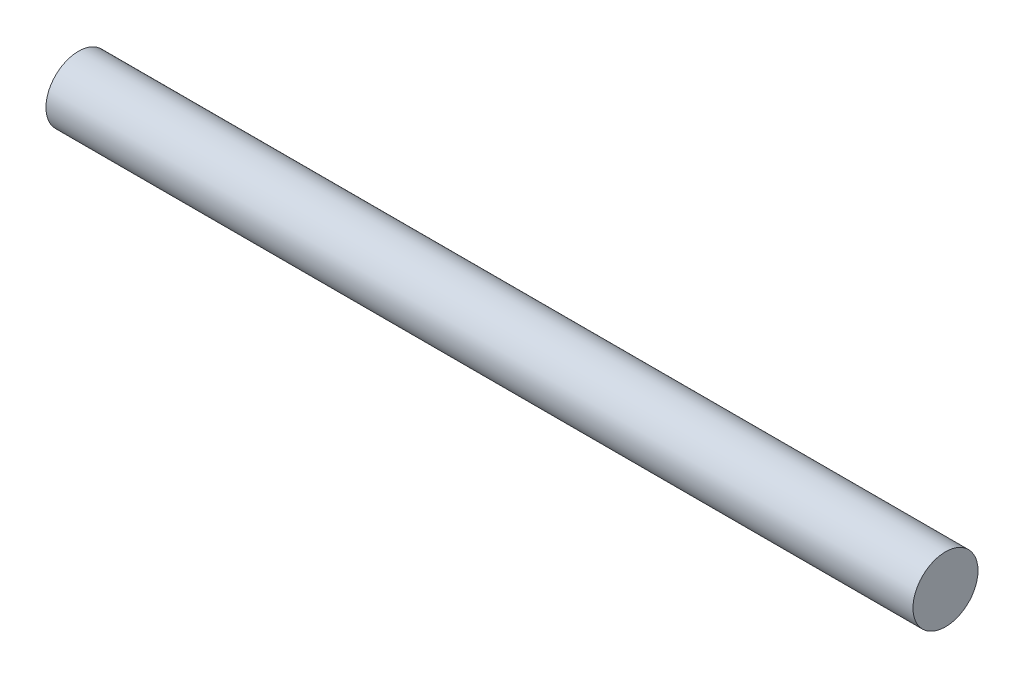
SolidWorks part; units mm, degrees
material "6061-T6 (SS)"
ref_plane "Front Plane" through (0, 0, 0) normal (0, 0, 1) x (1, 0, 0)
ref_plane "Top Plane" through (0, 0, 0) normal (0, 1, 0) x (1, 0, 0)
ref_plane "Right Plane" through (0, 0, 0) normal (1, 0, 0) x (0, 0, -1)
sketch "Sketch1" plane through (0, 0, 0) normal (1, 0, 0) x (0, 0, -1)
  circle A0 centre (0, 0) radius 4.7625
  dimension "D1" = 9.525
extrude "Boss-Extrude1" add sketch "Sketch1" along normal blind 127
